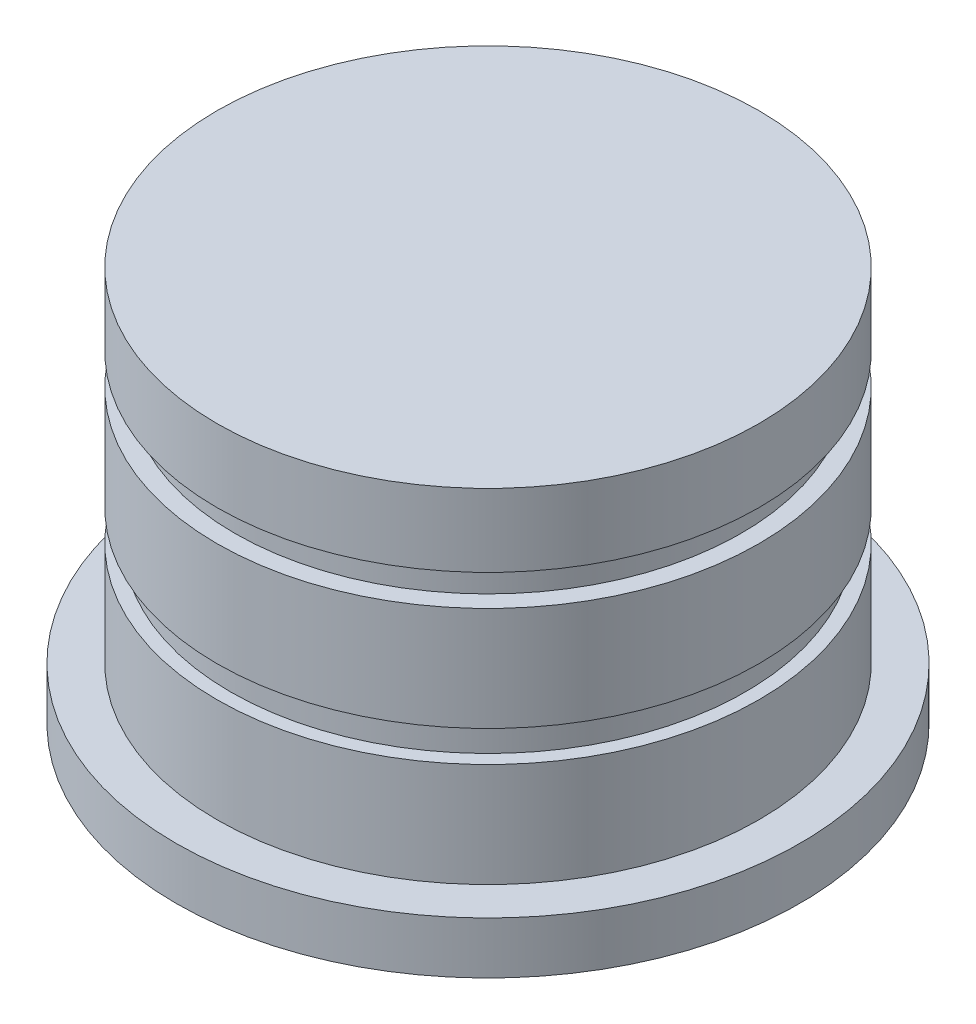
SolidWorks part; units mm, degrees
ref_plane "Front Plane" through (0, 0, 0) normal (0, 0, 1) x (1, 0, 0)
ref_plane "Top Plane" through (0, 0, 0) normal (0, 1, 0) x (1, 0, 0)
ref_plane "Right Plane" through (0, 0, 0) normal (1, 0, 0) x (0, 0, -1)
sketch "Sketch1" plane through (0, 0, 0) normal (0, 1, 0) x (1, 0, 0)
  circle A0 centre (0, 0) radius 3000
extrude "Boss-Extrude1" add sketch "Sketch1" along normal blind 500
sketch "Sketch2" plane through (0, 500, 0) normal (0, 1, 0) x (1, 0, 0)
  circle A0 centre (0, 0) radius 2606.5121
extrude "Boss-Extrude2" add sketch "Sketch2" along normal blind 1000 separate body
sketch "Sketch3" plane through (0, 1500, 0) normal (0, 1, 0) x (1, 0, 0)
  circle A0 centre (0, 0) radius 2476.5641
extrude "Boss-Extrude3" add sketch "Sketch3" along normal blind 300
sketch "Sketch4" plane through (0, 1800, 0) normal (0, 1, 0) x (1, 0, 0)
  circle A0 centre (0, 0) radius 2606.5121
extrude "Boss-Extrude4" add sketch "Sketch4" along normal blind 1000
sketch "Sketch5" plane through (0, 2800, 0) normal (0, 1, 0) x (1, 0, 0)
  circle A0 centre (0, 0) radius 2435.4277
extrude "Boss-Extrude5" add sketch "Sketch5" along normal blind 300
sketch "Sketch6" plane through (0, 3100, 0) normal (0, 1, 0) x (1, 0, 0)
  circle A0 centre (0, 0) radius 2606.5121
extrude "Boss-Extrude6" add sketch "Sketch6" along normal blind 700
